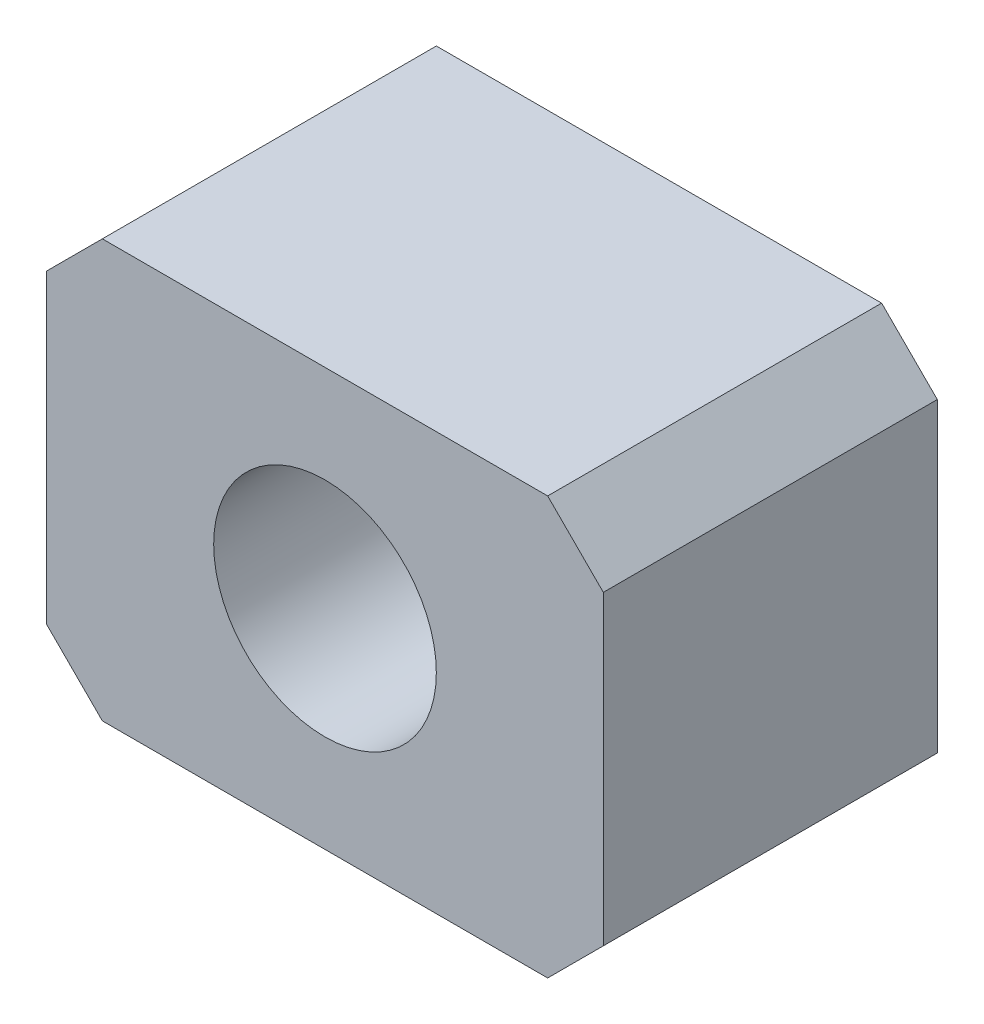
SolidWorks part; units mm, degrees
ref_plane "Front Plane" through (0, 0, 0) normal (0, 0, 1) x (1, 0, 0)
ref_plane "Top Plane" through (0, 0, 0) normal (0, 1, 0) x (1, 0, 0)
ref_plane "Right Plane" through (0, 0, 0) normal (1, 0, 0) x (0, 0, -1)
sketch "Sketch1" plane through (0, 0, 0) normal (0, 0, 1) x (1, 0, 0)
  line L0 (-10, 7.5) -> (-10, -7.5)
  line L1 (-10, 7.5) -> (10, 7.5)
  line L2 (-10, -7.5) -> (10, -7.5)
  line L3 (10, 7.5) -> (10, -7.5)
  line L4 (-10, 7.5) -> (10, -7.5) construction
  dimension "D1" = 20
  dimension "D2" = 15
extrude "Boss-Extrude1" add sketch "Sketch1" along normal blind 12
sketch "Sketch2" plane through (0, 0, 12) normal (0, 0, 1) x (1, 0, 0)
  circle A1 centre (0, 0) radius 4
  dimension "D3" = 8
extrude "Cut-Extrude1" cut sketch "Sketch2" against normal through all
chamfer "Chamfer1" distance 2 angle 45 4 edges at (-10, 7.5, 6) (-10, -7.5, 6) (10, -7.5, 6) (10, 7.5, 6)
